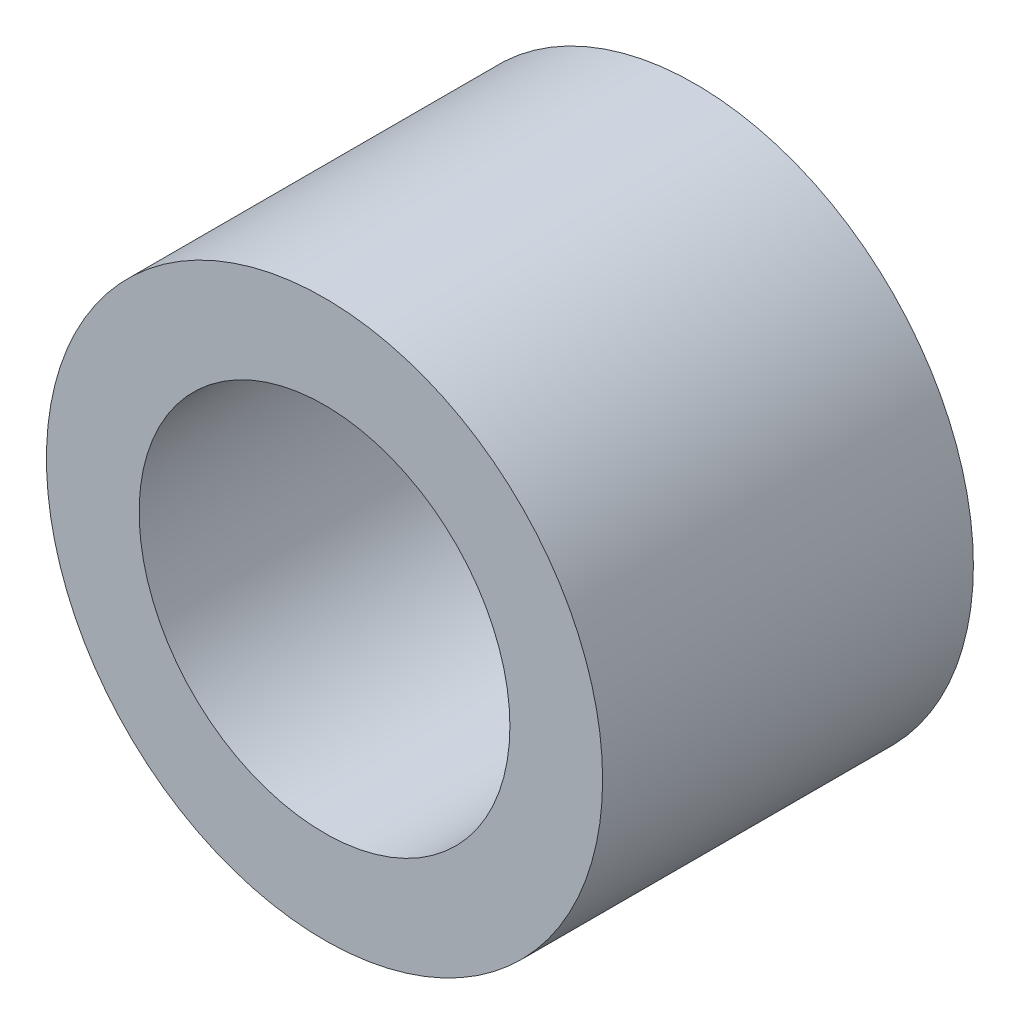
SolidWorks part; units mm, degrees
ref_plane "Plan de face" through (0, 0, 0) normal (0, 0, 1) x (1, 0, 0)
ref_plane "Plan de dessus" through (0, 0, 0) normal (0, 1, 0) x (1, 0, 0)
ref_plane "Plan de droite" through (0, 0, 0) normal (1, 0, 0) x (0, 0, -1)
sketch "Esquisse1" plane through (0, 0, 0) normal (0, 0, 1) x (1, 0, 0)
  circle A0 centre (0, 0) radius 3
  circle A1 centre (0, 0) radius 2
extrude "Extrusion1" add sketch "Esquisse1" along normal blind 4
